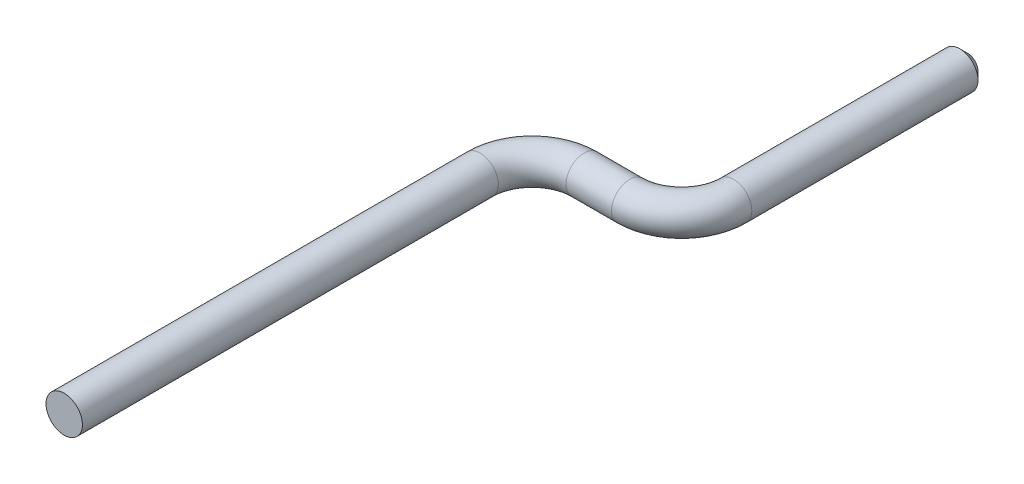
SolidWorks part; units mm, degrees
ref_plane "Front Plane" through (0, 0, 0) normal (0, 0, 1) x (1, 0, 0)
ref_plane "Top Plane" through (0, 0, 0) normal (0, 1, 0) x (1, 0, 0)
ref_plane "Right Plane" through (0, 0, 0) normal (1, 0, 0) x (0, 0, -1)
sketch "Sketch1" plane through (0, 0, 0) normal (0, 1, 0) x (1, 0, 0)
  line L0 (0, 0) -> (0, 16)
  line L1 (2, 18) -> (3.75, 18)
  line L2 (5.75, 20) -> (5.75, 29)
  arc A0 (3.75, 18) -> (5.75, 20) centre (3.75, 20) ccw
  arc A1 (0, 16) -> (2, 18) centre (2, 16) cw
  point P8 (5.75, 18)
  point P11 (0, 18)
  dimension "D4" = 2
  dimension "D1" = 18
  dimension "D2" = 5.75
  dimension "D3" = 11
sketch "Sketch2" plane through (0, 0, 0) normal (0, 0, 1) x (1, 0, 0)
  circle A0 centre (0, 0) radius 0.7
  dimension "D1" = 1.4
sweep "Sweep1" add profiles "Sketch2" path "Sketch1"
chamfer "Chamfer1" distance 0.3 angle 45 1 edges at (6.45, 0, -29)
